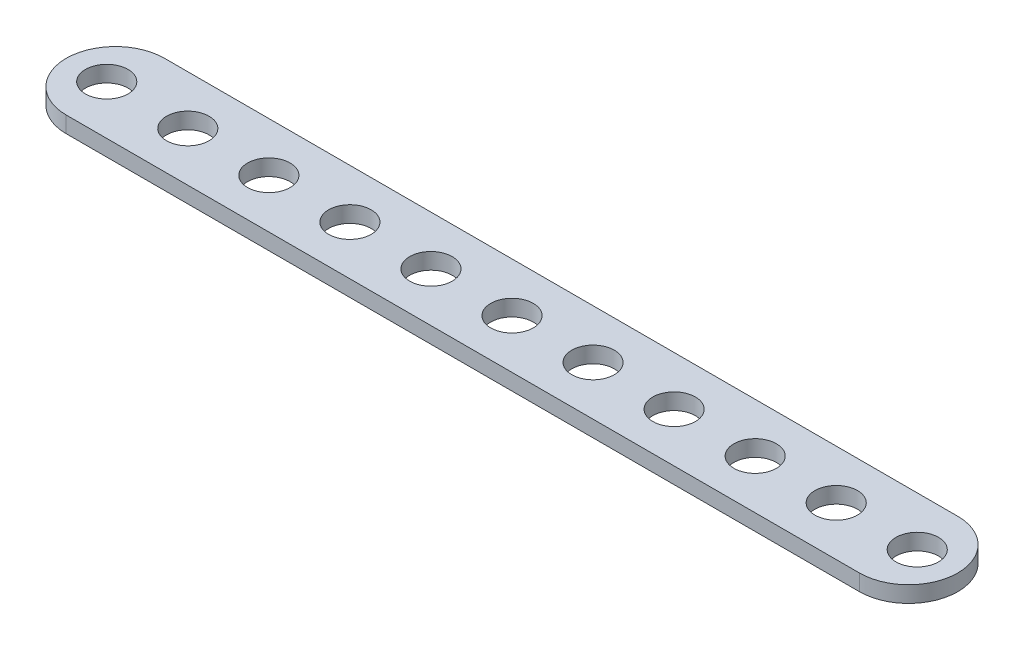
SolidWorks part; units mm, degrees
material "1060 Alloy"
ref_plane "Front Plane" through (0, 0, 0) normal (0, 0, 1) x (1, 0, 0)
ref_plane "Top Plane" through (0, 0, 0) normal (0, 1, 0) x (1, 0, 0)
ref_plane "Right Plane" through (0, 0, 0) normal (1, 0, 0) x (0, 0, -1)
sketch "Sketch1" plane through (0, 0, 0) normal (0, 1, 0) x (1, 0, 0)
  line L0 (4.85, 0) -> (83.15, 0) construction
  line L1 (4.85, 4.85) -> (83.15, 4.85)
  line L2 (4.85, -4.85) -> (83.15, -4.85)
  arc A0 (4.85, 4.85) -> (4.85, -4.85) centre (4.85, 0) ccw
  arc A1 (83.15, -4.85) -> (83.15, 4.85) centre (83.15, 0) ccw
  point P3 (44, 0)
  dimension "D2" = 88
  dimension "D1" = 9.7
extrude "Boss-Extrude1" add sketch "Sketch1" along normal blind 1.6
sketch "Sketch2" plane through (0, 1.6, 0) normal (0, 1, 0) x (1, 0, 0)
  line L0 (-3.846, 0) -> (27.4208, 0) construction
  line L1 (4.85, -4.85) -> (83.15, -4.85) construction
  circle A0 centre (4, 0) radius 2.1
  arc A1 (4.85, 4.85) -> (4.85, -4.85) centre (4.85, 0) ccw construction
  point P2 (0, 0)
  dimension "D2" = 4.2
  dimension "D1" = 4
extrude "Cut-Extrude1" cut sketch "Sketch2" against normal through all
pattern_linear "LPattern1" count 11 spacing 8 along (1, 0, 0) of "Cut-Extrude1"
